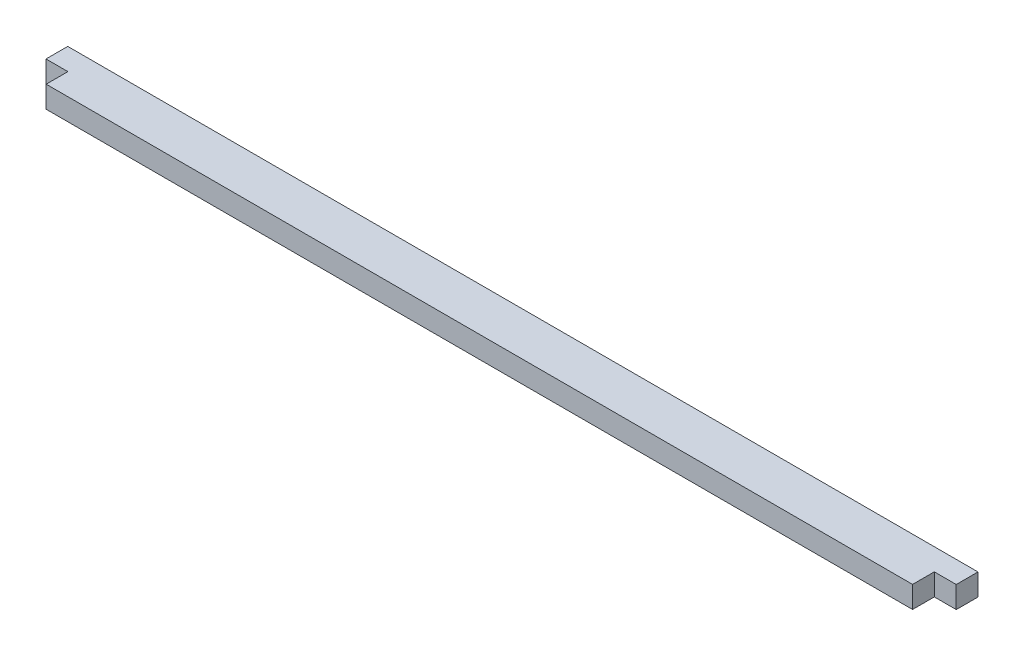
SolidWorks part; units mm, degrees
ref_plane "Front" through (0, 0, 0) normal (0, 0, 1) x (1, 0, 0)
ref_plane "Top" through (0, 0, 0) normal (0, 1, 0) x (1, 0, 0)
ref_plane "Right" through (0, 0, 0) normal (1, 0, 0) x (0, 0, -1)
sketch "Sketch2" plane through (0, 0, 0) normal (0, 1, 0) x (1, 0, 0)
  line L1 (3.2004, -6.35) -> (129.6543, -6.35)
  line L2 (0, -3.175) -> (0, 0)
  line L3 (0, 0) -> (132.8547, 0)
  line L4 (132.8547, -3.175) -> (132.8547, 0)
  line L9 (0, -3.175) -> (3.2004, -3.175)
  line L10 (3.2004, -6.35) -> (3.2004, -3.175)
  line L13 (132.8547, -3.175) -> (129.6543, -3.175)
  line L14 (129.6543, -6.35) -> (129.6543, -3.175)
  point P0 (0, 0)
  dimension "D1" = 132.8547
  dimension "D2" = 3.175
  dimension "D3" = 3.175
  dimension "D4" = 3.2004
extrude "Boss-Extrude1" add sketch "Sketch2" along normal blind 3.175
equation "\"D1@Sketch2\"= 4.62075 + 0.25 + 0.25 + 0.016 + ( 6 / 64 )"
